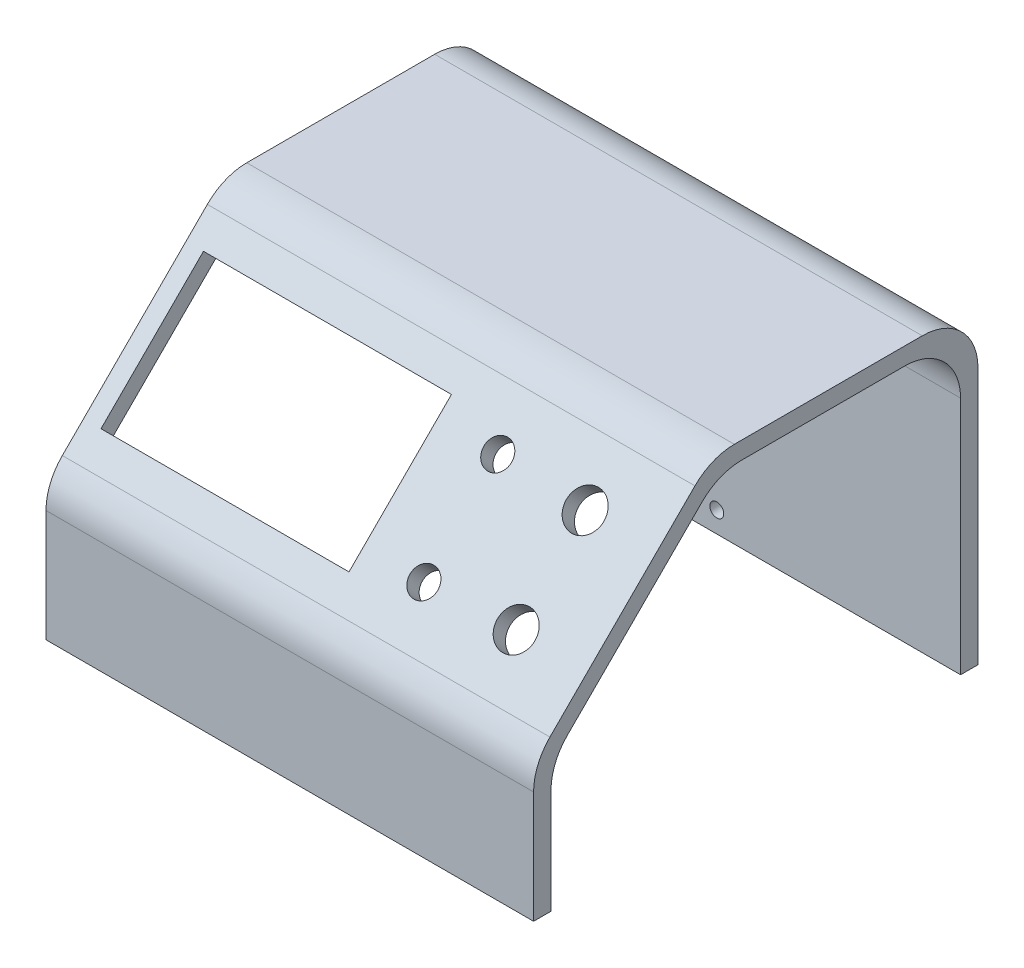
SolidWorks part; units mm, degrees
ref_plane "Front Plane" through (0, 0, 0) normal (0, 0, 1) x (1, 0, 0)
ref_plane "Top Plane" through (0, 0, 0) normal (0, 1, 0) x (1, 0, 0)
ref_plane "Right Plane" through (0, 0, 0) normal (1, 0, 0) x (0, 0, -1)
sketch "Sketch1" plane through (0, 0, 0) normal (1, 0, 0) x (0, 0, -1)
  line L0 (0, 0) -> (0, 23.3151)
  line L1 (0, 23.3151) -> (30.5329, 53.848)
  line L2 (30.5329, 53.848) -> (74.676, 53.848)
  line L3 (74.676, 53.848) -> (74.676, 0)
  line L4 (74.676, 0) -> (77.851, 0)
  line L5 (77.851, 0) -> (77.851, 57.023)
  line L6 (77.851, 57.023) -> (29.2177, 57.023)
  line L7 (29.2177, 57.023) -> (-3.175, 24.6303)
  line L8 (-3.175, 24.6303) -> (-3.175, 0)
  line L9 (-3.175, 0) -> (0, 0)
  dimension "D1" = 53.848
  dimension "D2" = 74.676
  dimension "D3" = 3.175
  dimension "D4" = 3.175
  dimension "D5" = 135
  dimension "D6" = 43.18
  dimension "D7" = 3.175
  dimension "D8" = 3.175
extrude "Boss-Extrude1" add sketch "Sketch1" along normal blind 88.9
fillet "Fillet1" radius 10.16 6 edges at (44.45, 23.3151, 0) (44.45, 24.6303, 3.175) (44.45, 53.848, -30.5329) (44.45, 57.023, -29.2177) (44.45, 53.848, -74.676) (44.45, 57.023, -77.851)
sketch "Sketch2" plane through (0, 13.9026, 13.9026) normal (0, 0.7071, 0.7071) x (1, 0, 0)
  line L0 (0, 56.773) -> (0, 19.3796) construction
  line L1 (3.175, 51.2843) -> (48.387, 51.2843)
  line L2 (3.175, 51.2843) -> (3.175, 24.8683)
  line L3 (3.175, 24.8683) -> (48.387, 24.8683)
  line L4 (48.387, 51.2843) -> (48.387, 24.8683)
  line L5 (88.9, 56.773) -> (88.9, 19.3796) construction
  line L6 (75.819, 46.9663) -> (75.819, 29.1863) construction
  line L7 (59.436, 47.6013) -> (59.436, 28.5513) construction
  circle A0 centre (75.819, 46.9663) radius 3.429
  circle A1 centre (75.819, 29.1863) radius 3.429
  circle A2 centre (59.436, 47.6013) radius 2.54
  circle A3 centre (59.436, 28.5513) radius 2.54
  point P6 (48.387, 38.0763)
  point P9 (88.9, 38.0763)
  point P14 (75.819, 38.0763)
  point P19 (59.436, 38.0763)
  dimension "D4" = 6.858
  dimension "D5" = 6.858
  dimension "D8" = 5.08
  dimension "D9" = 5.08
  dimension "D1" = 45.212
  dimension "D2" = 26.416
  dimension "D3" = 3.175
  dimension "D6" = 17.78
  dimension "D10" = 19.05
  dimension "D11" = 11.049
  dimension "D12" = 16.383
extrude "Cut-Extrude1" cut sketch "Sketch2" against normal up to next
sketch "Sketch4" plane through (0, 0, -77.851) normal (0, 0, -1) x (-1, 0, 0)
  line L0 (0, 46.863) -> (-88.9, 46.863) construction
  line L1 (-3.175, 43.688) -> (-31.115, 43.688)
  line L2 (-3.175, 43.688) -> (-3.175, 18.288)
  line L3 (-3.175, 18.288) -> (-31.115, 18.288)
  line L4 (-31.115, 43.688) -> (-31.115, 18.288)
  line L5 (0, 0) -> (0, 46.863) construction
  line L6 (-88.9, 0) -> (0, 0) construction
  circle A0 centre (-44.45, 3.81) radius 1.27
  point P12 (0, 0)
  point P13 (-44.45, 0)
  dimension "D5" = 2.54
  dimension "D1" = 3.175
  dimension "D2" = 3.175
  dimension "D3" = 27.94
  dimension "D4" = 25.4
  dimension "D6" = 3.81
extrude "Cut-Extrude3" cut sketch "Sketch4" against normal up to next
